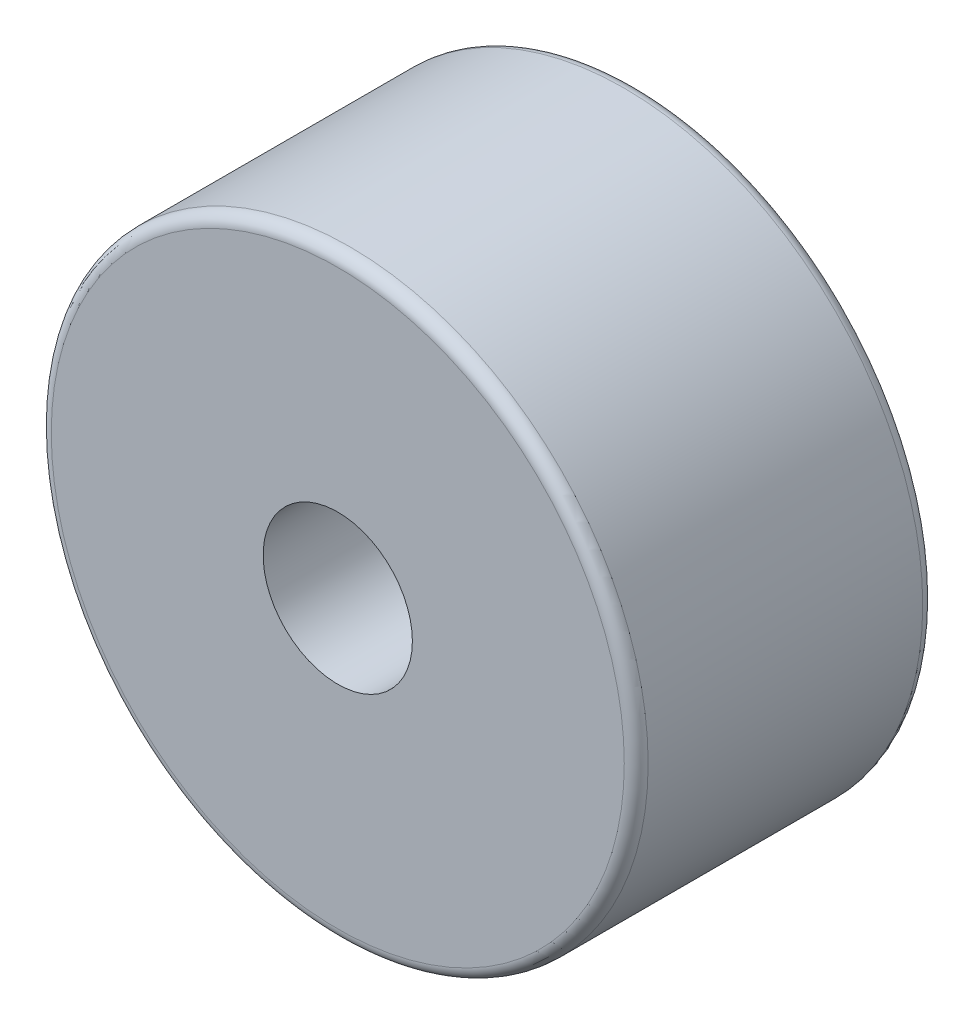
SolidWorks part; units mm, degrees
ref_plane "Front Plane" through (0, 0, 0) normal (0, 0, 1) x (1, 0, 0)
ref_plane "Top Plane" through (0, 0, 0) normal (0, 1, 0) x (1, 0, 0)
ref_plane "Right Plane" through (0, 0, 0) normal (1, 0, 0) x (0, 0, -1)
sketch "Sketch1" plane through (0, 0, 0) normal (0, 1, 0) x (1, 0, 0)
  line L0 (0, 0) -> (0, 4.8042) construction
  line L1 (-1.5875, 0) -> (-6.35, 0)
  line L2 (-6.35, 0) -> (-6.35, 6.35)
  line L3 (-6.35, 6.35) -> (-2.9718, 6.35)
  line L4 (-1.5875, 0) -> (-1.5875, 2.3813)
  line L5 (-1.5875, 2.3813) -> (-2.9718, 2.3813)
  line L6 (-2.9718, 2.3813) -> (-2.9718, 6.35)
  dimension "D1" = 2.9718
  dimension "D2" = 6.35
  dimension "D4" = 2.3813
  dimension "D5" = 6.35
revolve "Revolve1" add sketch "Sketch1" angle 360 about L0
fillet "Fillet1" radius 0.254 2 edges at (6.35, 0, 0) (6.35, 0, -6.35)
